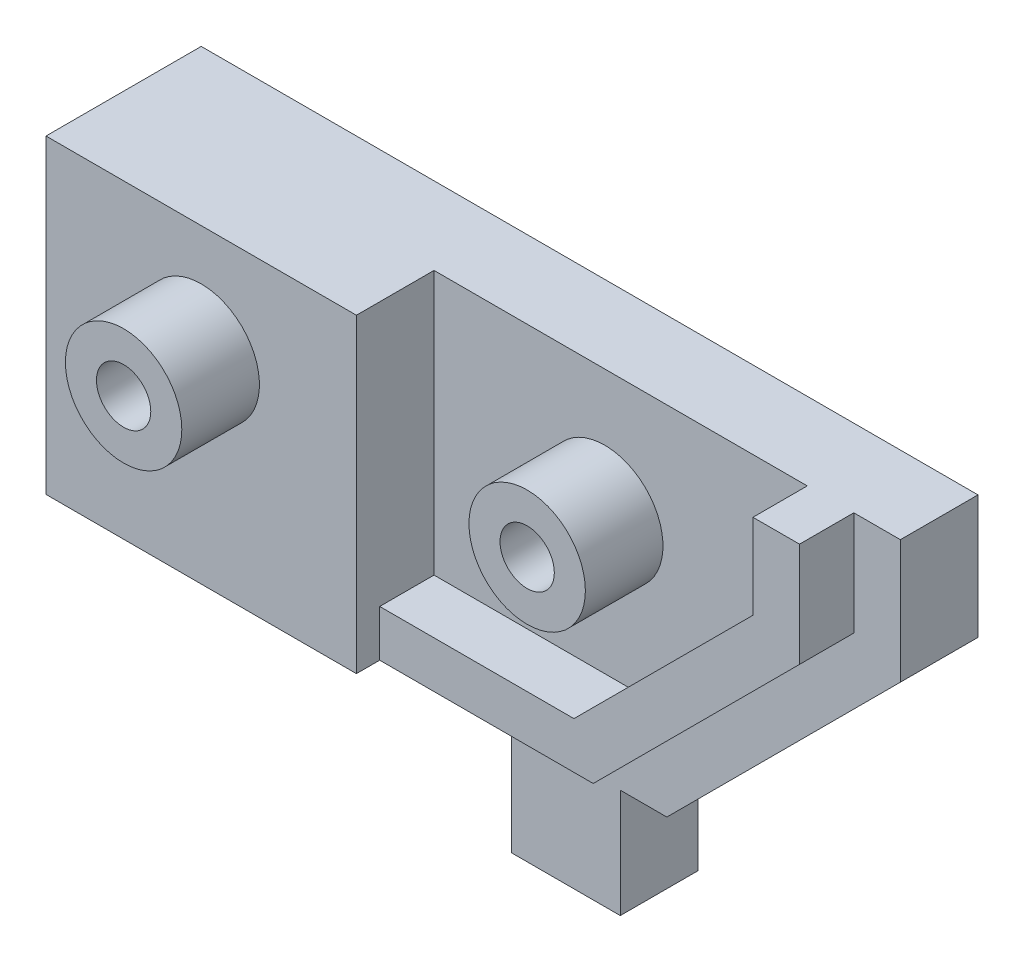
SolidWorks part; units mm, degrees
ref_plane "Front Plane" through (0, 0, 0) normal (0, 0, 1) x (1, 0, 0)
ref_plane "Top Plane" through (0, 0, 0) normal (0, 1, 0) x (1, 0, 0)
ref_plane "Right Plane" through (0, 0, 0) normal (1, 0, 0) x (0, 0, -1)
sketch "Sketch1" plane through (0, 0, 0) normal (0, 1, 0) x (1, 0, 0)
  line L10 (-18, -5.5617) -> (-18, -10) construction
  line L11 (0, 0) -> (-18, 0)
  line L12 (0, 0) -> (0, -5)
  line L13 (0, -5) -> (-15, -5)
  line L14 (-18, 0) -> (-18, -5.5617) construction
  line L16 (-15, -5) -> (-15, -10)
  line L17 (-15, -10) -> (-35, -10)
  line L18 (-35, -5) -> (-35, -10)
  line L19 (-18, 0) -> (-22, 0)
  line L21 (-35, -5) -> (-35, 0)
  line L22 (-35, 0) -> (-22, 0)
  dimension "D1" = 20
  dimension "D2" = 5
  dimension "D3" = 5
  dimension "D4" = 18
  dimension "D7" = 15
extrude "Boss-Extrude1" add sketch "Sketch1" along normal blind 23
sketch "Sketch2" plane through (0, 0, 10) normal (0, 0, 1) x (1, 0, 0)
  line L0 (-35, 23) -> (-35, 0) construction
  line L1 (-35, 0) -> (-15, 0) construction
  line L2 (-15, 0) -> (0, 0) construction
  line L3 (0, 23) -> (0, 0) construction
  circle A0 centre (-25, 16) radius 1.75
  circle A1 centre (-4, 15) radius 1.75
  dimension "D5" = 3.5
  dimension "D6" = 3.5
  dimension "D1" = 10
  dimension "D2" = 16
  dimension "D3" = 15
  dimension "D4" = 4
extrude "Cut-Extrude1" cut sketch "Sketch2" against normal through all
sketch "Sketch3" plane through (0, 0, 0) normal (0, -1, 0) x (1, 0, 0)
  line L0 (-25, 10) -> (-25, 0) construction
  line L1 (-35, 10) -> (-15, 10) construction
  line L3 (0, 0) -> (-35, 0) construction
  line L5 (0, 2.5) -> (-35, 2.5) construction
  line L6 (0, 5) -> (0, 0) construction
  line L7 (-35, 0) -> (-35, 10) construction
  circle A1 centre (-25, 2.5) radius 1.5
  dimension "D1" = 3
extrude "Cut-Extrude2" cut sketch "Sketch3" against normal blind 10
sketch "Sketch4" plane through (0, 0, 0) normal (0, -1, 0) x (1, 0, 0)
  line L0 (-35, 2.5) -> (0, 2.5) construction
  line L2 (0, 5) -> (0, 0) construction
  line L3 (-35, 0) -> (-35, 10) construction
  line L6 (-15, 5) -> (0, 5) construction
  line L7 (-10, 0) -> (-3, 0)
  line L8 (-10, 0) -> (-10, 5)
  line L9 (-10, 5) -> (-3, 5)
  line L10 (-3, 0) -> (-3, 5)
  line L11 (-10, 0) -> (-3, 5) construction
  line L12 (-10, 5) -> (-3, 0) construction
  point P12 (-6.5, 2.5)
  dimension "D1" = 7
  dimension "D3" = 3
extrude "Boss-Extrude2" add sketch "Sketch4" along normal blind 7
sketch "Sketch5" plane through (0, 0, 10) normal (0, 0, 1) x (1, 0, 0)
  circle A0 centre (-25, 16) radius 1.75
  circle A1 centre (-25, 16) radius 3.75
  circle A2 centre (-25, 16) radius 1.75 construction
  dimension "D1" = 2
extrude "Boss-Extrude3" add sketch "Sketch5" along normal blind 5
sketch "Sketch6" plane through (0, 0, 5) normal (0, 0, 1) x (1, 0, 0)
  circle A0 centre (-4, 15) radius 1.75
  circle A1 centre (-4, 15) radius 1.75 construction
  circle A2 centre (-4, 15) radius 3.75
  dimension "D1" = 2
extrude "Boss-Extrude4" add sketch "Sketch6" along normal blind 5
sketch "Sketch7" plane through (0, 0, 5) normal (0, 0, 1) x (1, 0, 0)
  line L0 (0, 0) -> (0, 23)
  line L1 (0, 23) -> (15.0472, 23)
  line L2 (15.0472, 15.0472) -> (0, 0)
  line L3 (15.0472, 23) -> (15.0472, 15.0472)
  dimension "D1" = 45
  dimension "D2" = 21.28
extrude "Boss-Extrude5" add sketch "Sketch7" against normal blind 5
sketch "Sketch8" plane through (0, 0, 5) normal (0, 0, 1) x (1, 0, 0)
  line L0 (12.0472, 23) -> (12.0472, 16.2899)
  line L1 (-15, 23) -> (15.0472, 23) construction
  line L2 (12.0472, 16.2899) -> (-1.2426, 3)
  line L3 (-1.2426, 3) -> (-15, 3)
  line L4 (-15, 23) -> (-15, 0) construction
  line L5 (15.0472, 15.0472) -> (15.0472, 23) construction
  line L6 (0, 0) -> (15.0472, 15.0472) construction
  line L7 (-15, 0) -> (-10, 0) construction
  line L8 (9.0472, 23) -> (9.0472, 17.5325)
  line L9 (9.0472, 17.5325) -> (-2.4853, 6)
  line L10 (-2.4853, 6) -> (-15, 6)
  line L11 (9.0472, 23) -> (12.0472, 23)
  line L12 (-15, 6) -> (-15, 3)
  dimension "D1" = 3
  dimension "D2" = 3
  dimension "D3" = 3
  dimension "D4" = 3
extrude "Boss-Extrude6" add sketch "Sketch8" along normal blind 3.5
sketch "Sketch9" plane through (-15, 0, 0) normal (1, 0, 0) x (0, 0, -1)
  line L1 (-5, 3) -> (-10, 3)
  line L2 (-5, 3) -> (-5, 0)
  line L3 (-5, 0) -> (-10, 0)
  line L4 (-10, 3) -> (-10, 0)
extrude "Cut-Extrude3" cut sketch "Sketch9" against normal up to surface (20 mm away) contours L2 L1 L4 L3 up to face at (-35, 11.5, 5)
